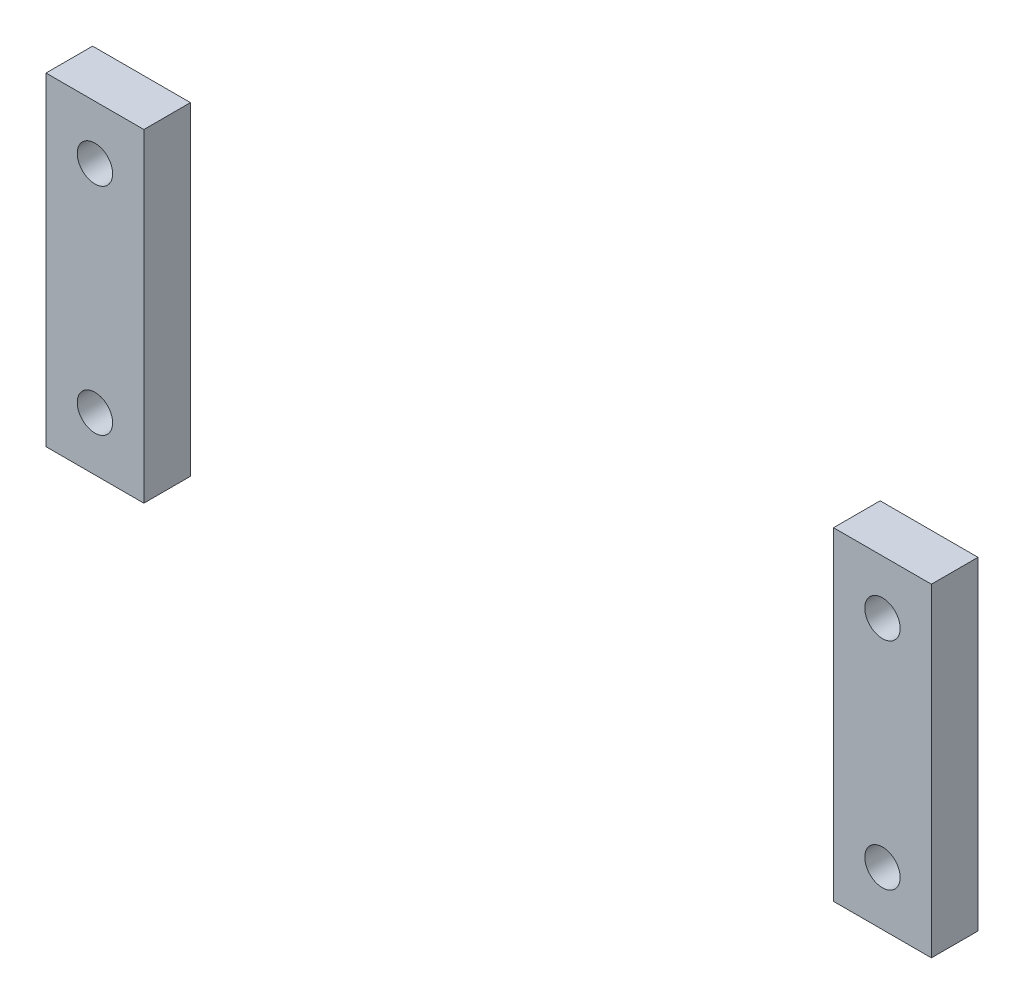
SolidWorks part; units mm, degrees
ref_plane "Front Plane" through (0, 0, 0) normal (0, 0, 1) x (1, 0, 0)
ref_plane "Top Plane" through (0, 0, 0) normal (0, 1, 0) x (1, 0, 0)
ref_plane "Right Plane" through (0, 0, 0) normal (1, 0, 0) x (0, 0, -1)
sketch "Sketch1" plane through (0, 0, 3) normal (0, 0, 1) x (1, 0, 0)
  line L13 (47.5, 0) -> (-47.5, 0) construction
  line L14 (-47.5, 23.15) -> (-47.5, -23.15) construction
  line L15 (0, 23.15) -> (0, -23.15) construction
  line L16 (47.5, -17.3625) -> (47.5, 17.3625)
  line L17 (47.5, 23.15) -> (47.5, -23.15) construction
  line L18 (47.5, 17.3625) -> (37, 17.3625)
  line L19 (37, 17.3625) -> (37, -17.3625)
  line L20 (37, 8.15) -> (37, -8.15) construction
  line L21 (47.5, -17.3625) -> (37, -17.3625)
  line L22 (-47.5, -17.3625) -> (-37, -17.3625)
  line L23 (-37, 17.3625) -> (-37, -17.3625)
  line L24 (-47.5, 17.3625) -> (-37, 17.3625)
  line L25 (-47.5, -17.3625) -> (-47.5, 17.3625)
  line L26 (42.25, 0) -> (42.25, 5.7875) construction
  line L27 (42.25, 23.15) -> (42.25, -23.15) construction
  line L28 (42.25, 5.7875) -> (42.25, 11.575) construction
  line L29 (42.25, 11.575) -> (42.25, 17.3625) construction
  line L30 (42.25, 17.3625) -> (42.25, 23.15) construction
  point P16 (37, 0)
extrude "Boss-Extrude1" add sketch "Sketch1" along normal blind 5
hole_wizard "#6 Clearance Hole2" positions "Sketch6" profile "Sketch7" hole size "#6" standard "ANSI Inch" end condition through all
sketch "Sketch6" plane through (0, 0, 8) normal (0, 0, 1) x (1, 0, 0)
  point P0 (42.25, 11.575)
  point P3 (42.25, -11.575)
  point P6 (-42.25, 11.575)
  point P9 (-42.25, -11.575)
sketch "Sketch7" plane through (42.25, 11.575, 8) normal (1, 0, 0) x (0, -1, 0)
  line L0 (0, 0) -> (0, 5)
  line L1 (0, 5) -> (1.8986, 5)
  line L2 (1.8986, 5) -> (1.8986, 0)
  line L5 (1.8986, 0) -> (0, 0)
  line L11 (0, -6.35) -> (0, 107.95) construction
  dimension "Thru Hole Dia." = 3.7973
  dimension "Thru Hole Depth" = 5
